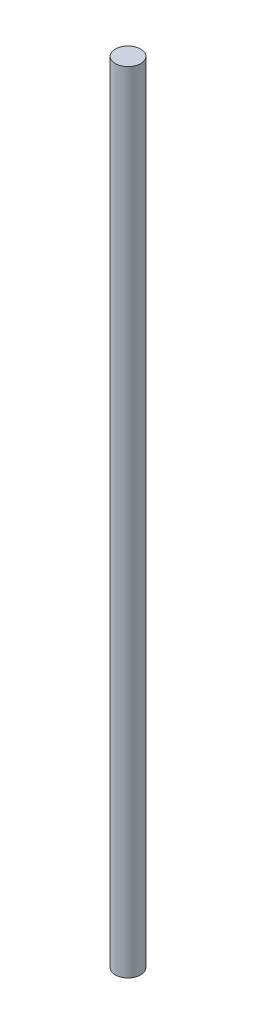
SolidWorks part; units mm, degrees
ref_plane "Alzado" through (0, 0, 0) normal (0, 0, 1) x (1, 0, 0)
ref_plane "Planta" through (0, 0, 0) normal (0, 1, 0) x (1, 0, 0)
ref_plane "Vista lateral" through (0, 0, 0) normal (1, 0, 0) x (0, 0, -1)
sketch "Croquis1" plane through (0, 0, 0) normal (0, 1, 0) x (1, 0, 0)
  circle A0 centre (0, 0) radius 4
  dimension "D1" = 8
extrude "Saliente-Extruir1" add sketch "Croquis1" along normal blind 250
